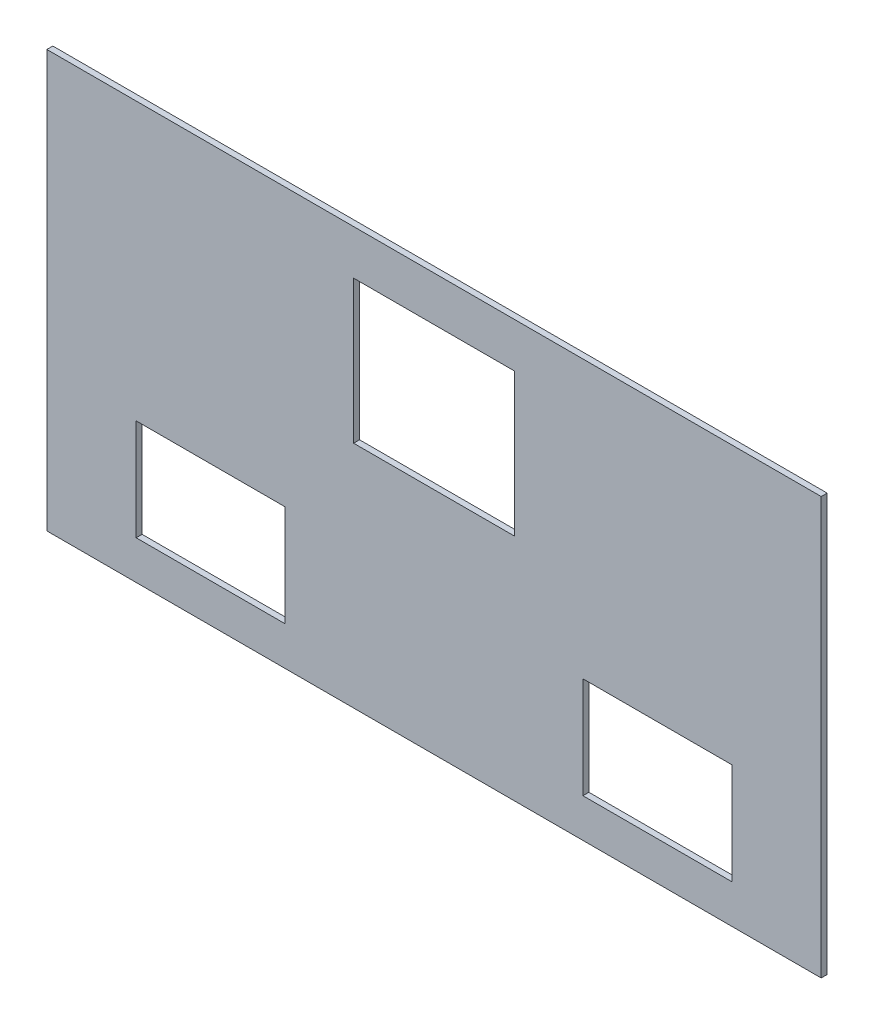
SolidWorks part; units mm, degrees
ref_plane "Front Plane" through (0, 0, 0) normal (0, 0, 1) x (1, 0, 0)
ref_plane "Top Plane" through (0, 0, 0) normal (0, 1, 0) x (1, 0, 0)
ref_plane "Right Plane" through (0, 0, 0) normal (1, 0, 0) x (0, 0, -1)
sketch "Sketch1" plane through (0, 0, 0) normal (0, 0, 1) x (1, 0, 0)
  line L1 (-65, -35) -> (65, -35)
  line L2 (-65, -35) -> (-65, 35)
  line L3 (-65, 35) -> (65, 35)
  line L4 (65, -35) -> (65, 35)
  line L5 (-65, -35) -> (65, 35) construction
  line L6 (-65, 35) -> (65, -35) construction
  point P0 (0, 0)
  dimension "D1" = 130
  dimension "D2" = 70
extrude "Boss-Extrude1" add sketch "Sketch1" along normal blind 1
sketch "Sketch2" plane through (0, 0, 1) normal (0, 0, 1) x (1, 0, 0)
  line L0 (-65, 35) -> (-65, -35) construction
  line L1 (-50, -28.5) -> (-25, -28.5)
  line L2 (-50, -28.5) -> (-50, -11.5)
  line L3 (-50, -11.5) -> (-25, -11.5)
  line L4 (-25, -28.5) -> (-25, -11.5)
  line L5 (-50, -28.5) -> (-25, -11.5) construction
  line L6 (-50, -11.5) -> (-25, -28.5) construction
  line L7 (25, -28.5) -> (50, -28.5)
  line L8 (25, -28.5) -> (25, -11.5)
  line L9 (25, -11.5) -> (50, -11.5)
  line L10 (50, -28.5) -> (50, -11.5)
  line L11 (25, -28.5) -> (50, -11.5) construction
  line L12 (25, -11.5) -> (50, -28.5) construction
  line L13 (-13.5, 3.5) -> (13.5, 3.5)
  line L14 (-13.5, 3.5) -> (-13.5, 27.5)
  line L15 (-13.5, 27.5) -> (13.5, 27.5)
  line L16 (13.5, 3.5) -> (13.5, 27.5)
  line L17 (-13.5, 3.5) -> (13.5, 27.5) construction
  line L18 (-13.5, 27.5) -> (13.5, 3.5) construction
  line L19 (65, -35) -> (65, 35) construction
  line L20 (-65, -35) -> (65, -35) construction
  line L21 (65, 35) -> (-65, 35) construction
  point P0 (-37.5, -20)
  point P5 (37.5, -20)
  point P10 (0, 15.5)
  point P15 (-50, -20)
  dimension "D1" = 15
  dimension "D2" = 15
  dimension "D3" = 25
  dimension "D4" = 25
  dimension "D5" = 15
  dimension "D6" = 15
  dimension "D7" = 17
  dimension "D8" = 17
  dimension "D9" = 25
  dimension "D10" = 25
  dimension "D11" = 7.5
  dimension "D12" = 27
  dimension "D13" = 24
extrude "Cut-Extrude1" cut sketch "Sketch2" against normal through all
